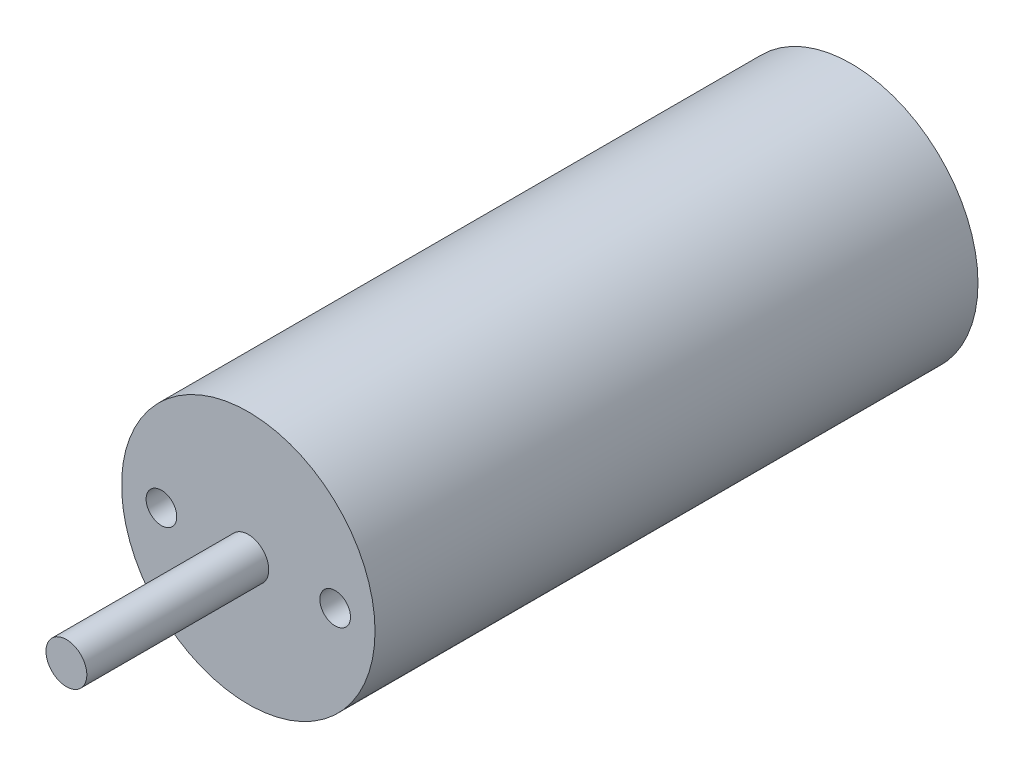
SolidWorks part; units mm, degrees
ref_plane "Front Plane" through (0, 0, 0) normal (0, 0, 1) x (1, 0, 0)
ref_plane "Top Plane" through (0, 0, 0) normal (0, 1, 0) x (1, 0, 0)
ref_plane "Right Plane" through (0, 0, 0) normal (1, 0, 0) x (0, 0, -1)
sketch "Sketch1" plane through (0, 0, 0) normal (0, 0, 1) x (1, 0, 0)
  circle A0 centre (12.4, 0) radius 12.4
  dimension "D1" = 24.8
extrude "Boss-Extrude1" add sketch "Sketch1" along normal blind 59
sketch "Sketch2" plane through (0, 0, 59) normal (0, 0, 1) x (1, 0, 0)
  line L0 (0, 0) -> (24.8, 0) construction
  circle A0 centre (12.4, 0) radius 12.4 construction
  circle A1 centre (12.4, 0) radius 2
  dimension "D1" = 4
extrude "Boss-Extrude2" add sketch "Sketch2" along normal blind 17.8
sketch "Sketch3" plane through (0, 0, 59) normal (0, 0, 1) x (1, 0, 0)
  line L0 (12.4, 12.4) -> (12.4, -12.4) construction
  circle A0 centre (20.9, 0) radius 1.5
  circle A1 centre (12.4, 0) radius 12.4 construction
  circle A2 centre (3.9, 0) radius 1.5
  dimension "D1" = 3
  dimension "D2" = 17
extrude "Cut-Extrude1" cut sketch "Sketch3" against normal blind 4.3942
